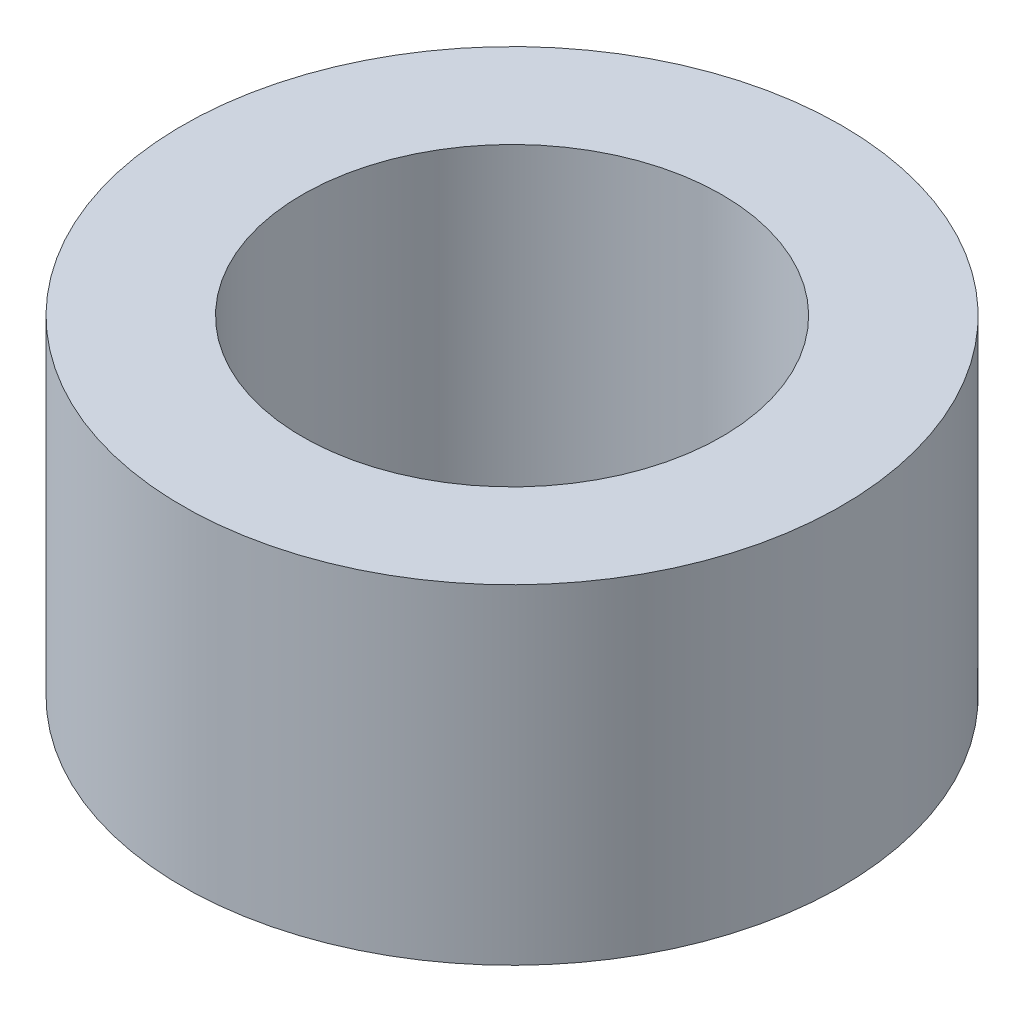
SolidWorks part; units mm, degrees
ref_plane "Plan de face" through (0, 0, 0) normal (0, 0, 1) x (1, 0, 0)
ref_plane "Plan de dessus" through (0, 0, 0) normal (0, 1, 0) x (1, 0, 0)
ref_plane "Plan de droite" through (0, 0, 0) normal (1, 0, 0) x (0, 0, -1)
sketch "Esquisse1" plane through (0, 0, 0) normal (0, 0, 1) x (1, 0, 0)
  line L0 (0, 0) -> (0, 6.0977) construction
  line L2 (3.5, 0) -> (5.5, 0)
  line L3 (3.5, 0) -> (3.5, 5.5)
  line L4 (3.5, 5.5) -> (5.5, 5.5)
  line L5 (5.5, 0) -> (5.5, 5.5)
  dimension "D1" = 3.5
  dimension "D2" = 5.5
  dimension "D3" = 5.5
revolve "Révolution1" add sketch "Esquisse1" angle 360 about L0
